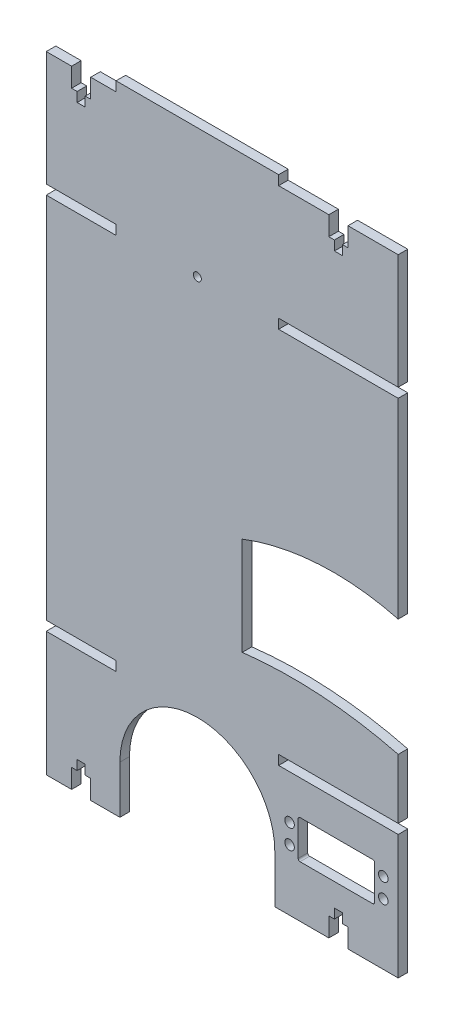
SolidWorks part; units mm, degrees
ref_plane "Front Plane" through (0, 0, 0) normal (0, 0, 1) x (1, 0, 0)
ref_plane "Top Plane" through (0, 0, 0) normal (0, 1, 0) x (1, 0, 0)
ref_plane "Right Plane" through (0, 0, 0) normal (1, 0, 0) x (0, 0, -1)
sketch "Sketch2" plane through (0, 0, 0) normal (0, 0, 1) x (1, 0, 0)
  line L1 (-92, 166.25) -> (92, 166.25)
  line L2 (-92, 166.25) -> (-92, -166.25)
  line L3 (-92, -166.25) -> (92, -166.25)
  line L4 (92, 166.25) -> (92, -166.25)
  line L5 (-92, 166.25) -> (92, -166.25) construction
  line L6 (-92, -166.25) -> (92, 166.25) construction
  point P0 (0, 0)
  dimension "D1" = 332.5
  dimension "D2" = 184
extrude "Boss-Extrude1" add sketch "Sketch2" along normal blind 5
sketch "Sketch3" plane through (0, 0, 5) normal (0, 0, 1) x (1, 0, 0)
  line L0 (-92, 166.25) -> (-92, -166.25) construction
  line L1 (-55.5, -101.25) -> (-92, -101.25)
  line L2 (-55.5, -101.25) -> (-55.5, -96.25)
  line L3 (-55.5, -96.25) -> (-92, -96.25)
  line L4 (-92, -101.25) -> (-92, -96.25)
  line L5 (-55.5, -101.25) -> (-92, -96.25) construction
  line L6 (-55.5, -96.25) -> (-92, -101.25) construction
  line L7 (-98, -96.25) -> (-55.5, -96.25) construction
  line L8 (92, -166.25) -> (92, 166.25) construction
  line L9 (29.5, -96.25) -> (92, -96.25)
  line L10 (29.5, -96.25) -> (29.5, -101.25)
  line L11 (29.5, -101.25) -> (92, -101.25)
  line L12 (92, -96.25) -> (92, -101.25)
  line L13 (29.5, -96.25) -> (92, -101.25) construction
  line L14 (29.5, -101.25) -> (92, -96.25) construction
  line L15 (29.5, -101.25) -> (92, -101.25) construction
  line L17 (29.5, 96.25) -> (92, 96.25) construction
  line L21 (-55.5, 161.25) -> (-92, 161.25)
  line L22 (-55.5, 161.25) -> (-55.5, 166.25)
  line L23 (-55.5, 166.25) -> (-92, 166.25)
  line L24 (-92, 161.25) -> (-92, 166.25)
  line L25 (-55.5, 161.25) -> (-92, 166.25) construction
  line L26 (-55.5, 166.25) -> (-92, 161.25) construction
  line L27 (29.5, 161.25) -> (92, 161.25)
  line L28 (29.5, 161.25) -> (29.5, 166.25)
  line L29 (29.5, 166.25) -> (92, 166.25)
  line L30 (92, 161.25) -> (92, 166.25)
  line L31 (29.5, 161.25) -> (92, 166.25) construction
  line L32 (29.5, 166.25) -> (92, 161.25) construction
  line L33 (29.5, 101.25) -> (92, 101.25)
  line L34 (27.5, -141.25) -> (27.5, -166.25)
  line L37 (-92, -166.25) -> (92, -166.25) construction
  line L38 (27.5, -166.25) -> (-53.5, -166.25)
  line L39 (-53.5, -166.25) -> (-53.5, -141.25)
  line L40 (29.5, 101.25) -> (29.5, 96.25)
  line L41 (29.5, 96.25) -> (92, 96.25)
  line L42 (92, 101.25) -> (92, 96.25)
  line L43 (29.5, 101.25) -> (92, 96.25) construction
  line L44 (29.5, 96.25) -> (92, 101.25) construction
  line L45 (-98, 101.25) -> (-55.5, 101.25) construction
  line L46 (-55.5, 96.25) -> (-92, 96.25)
  line L47 (-55.5, 96.25) -> (-55.5, 101.25)
  line L48 (-55.5, 101.25) -> (-92, 101.25)
  line L49 (-92, 96.25) -> (-92, 101.25)
  line L50 (-55.5, 96.25) -> (-92, 101.25) construction
  line L51 (-55.5, 101.25) -> (-92, 96.25) construction
  arc A2 (27.5, -141.25) -> (-53.5, -141.25) centre (-13, -141.25) ccw
  point P7 (-73.75, -98.75)
  point P17 (60.75, -98.75)
  point P32 (-73.75, 163.75)
  point P39 (60.75, 163.75)
  point P45 (60.75, 98.75)
  point P54 (-73.75, 98.75)
extrude "Cut-Extrude1" cut sketch "Sketch3" against normal blind 5
sketch "Sketch4" plane through (0, 0, 5) normal (0, 0, 1) x (1, 0, 0)
  line L0 (-73.75, 161.25) -> (-73.75, 123.1738) construction
  line L1 (-92, 161.25) -> (-55.5, 161.25) construction
  line L2 (69.7422, 161.25) -> (69.7422, -166.25) construction
  line L3 (-92, 0) -> (92, 0) construction
  line L5 (-13, 166.25) -> (-13, 111.1543) construction
  line L6 (29.5, 166.25) -> (-55.5, 166.25) construction
  line L7 (29.5, 161.25) -> (92, 161.25) construction
  line L8 (27.5, -166.25) -> (92, -166.25) construction
  line L9 (69.7422, -2.5) -> (44.3363, -2.5) construction
  line L10 (92, -96.25) -> (92, 96.25) construction
  line L11 (0, 0) -> (0, 111.1543) construction
  line L12 (0, 111.1543) -> (-13, 111.1543) construction
  line L13 (-6.5, 111.1543) -> (-6.5, 119.3244) construction
  line L14 (60.75, 161.25) -> (60.75, 140.689) construction
  line L15 (55.75, 161.25) -> (55.75, 151.25)
  line L16 (55.75, 151.25) -> (58.65, 151.25)
  line L17 (58.65, 151.25) -> (58.65, 146.25)
  line L18 (58.65, 146.25) -> (62.85, 146.25)
  line L19 (55.75, 161.25) -> (65.75, 161.25)
  line L20 (62.85, 151.25) -> (62.85, 146.25)
  line L21 (65.75, 151.25) -> (62.85, 151.25)
  line L22 (65.75, 161.25) -> (65.75, 151.25)
  line L23 (-78.75, 161.25) -> (-78.75, 151.25)
  line L24 (-78.75, 151.25) -> (-75.85, 151.25)
  line L25 (-75.85, 151.25) -> (-75.85, 146.25)
  line L26 (-68.75, 161.25) -> (-78.75, 161.25)
  line L27 (-71.65, 146.25) -> (-75.85, 146.25)
  line L28 (-71.65, 151.25) -> (-71.65, 146.25)
  line L29 (-68.75, 151.25) -> (-71.65, 151.25)
  line L30 (-68.75, 161.25) -> (-68.75, 151.25)
  line L31 (60.75, -166.25) -> (60.75, -145.689) construction
  line L32 (65.75, -166.25) -> (65.75, -156.25)
  line L33 (65.75, -156.25) -> (62.85, -156.25)
  line L34 (62.85, -156.25) -> (62.85, -151.25)
  line L35 (55.75, -166.25) -> (65.75, -166.25)
  line L36 (58.65, -151.25) -> (62.85, -151.25)
  line L37 (58.65, -156.25) -> (58.65, -151.25)
  line L38 (55.75, -156.25) -> (58.65, -156.25)
  line L39 (55.75, -166.25) -> (55.75, -156.25)
  line L40 (-68.75, -166.25) -> (-68.75, -156.25)
  line L41 (-68.75, -156.25) -> (-71.65, -156.25)
  line L42 (-71.65, -156.25) -> (-71.65, -151.25)
  line L43 (-71.65, -151.25) -> (-75.85, -151.25)
  line L44 (-68.75, -166.25) -> (-78.75, -166.25)
  line L45 (-75.85, -156.25) -> (-75.85, -151.25)
  line L46 (-78.75, -156.25) -> (-75.85, -156.25)
  line L47 (-78.75, -166.25) -> (-78.75, -156.25)
  point P36 (60.75, 146.25)
  point P46 (-73.75, 146.25)
  point P57 (60.75, -151.25)
  point P66 (-73.75, -151.25)
  dimension "D1" = 10
  dimension "D2" = 5
  dimension "D3" = 2.9
  dimension "D4" = 5
extrude "Cut-Extrude2" cut sketch "Sketch4" against normal blind 10
sketch "Sketch5" plane through (0, 0, 5) normal (0, 0, 1) x (1, 0, 0)
  line L0 (-55.5, 98.75) -> (29.5, 98.75) construction
  line L1 (-55.5, 96.25) -> (-55.5, 101.25) construction
  line L2 (29.5, 96.25) -> (29.5, 101.25) construction
  circle A0 centre (-13, 98.75) radius 2.1
  dimension "D1" = 4.2
extrude "Cut-Extrude3" cut sketch "Sketch5" against normal blind 10
sketch "Sketch6" plane through (0, 0, 0) normal (0, 0, -1) x (-1, 0, 0)
  line L0 (-78.2, -106.25) -> (-41.2, -106.25)
  line L1 (-41.2, -106.25) -> (-40.7, -106.25)
  line L2 (-39.7, -107.25) -> (-39.7, -125.25)
  line L3 (-40.7, -126.25) -> (-78.7, -126.25)
  line L4 (-79.7, -125.25) -> (-79.7, -107.25)
  line L5 (-78.7, -106.25) -> (-78.2, -106.25)
  circle A0 centre (-35.2, -111.17) radius 2.5
  circle A1 centre (-35.2, -121.33) radius 2.5
  circle A2 centre (-84.2, -111.17) radius 2.5
  circle A3 centre (-84.2, -121.33) radius 2.5
  arc A4 (-40.7, -106.25) -> (-39.7, -107.25) centre (-40.7, -107.25) cw
  arc A5 (-39.7, -125.25) -> (-40.7, -126.25) centre (-40.7, -125.25) cw
  arc A6 (-78.7, -126.25) -> (-79.7, -125.25) centre (-78.7, -125.25) cw
  arc A7 (-79.7, -107.25) -> (-78.7, -106.25) centre (-78.7, -107.25) cw
extrude "Cut-Extrude4" [suppressed] cut sketch "Sketch6" against normal blind 20
sketch "Sketch7" plane through (0, 0, 5) normal (0, 0, 1) x (1, 0, 0)
  line L4 (92.0183, -3.9595) -> (92, -22.8853)
  line L5 (92, -96.25) -> (92, 96.25) construction
  arc A4 (92.0183, -3.9595) -> (39.9761, 3.3554) centre (49.7, -116.25) ccw
  arc A5 (92, -22.8853) -> (36.0805, -14.6589) centre (49.7, -116.25) ccw
  arc A6 (39.9761, 3.3554) -> (36.0805, -14.6589) centre (102.0215, -19.4902) ccw
extrude "Cut-Extrude6" [suppressed] cut sketch "Sketch7" against normal through all
sketch "Esquisse1" plane through (0, 0, 0) normal (0, 0, -1) x (-1, 0, 0)
  line L0 (-84.2, -124.17) -> (-35.2, -124.17) construction
  line L1 (-84.2, -134.33) -> (-35.2, -134.33) construction
  line L2 (-29.5, -101.25) -> (-92, -101.25) construction
  line L4 (-40.7, -119.25) -> (-78.7, -119.25)
  line L5 (-39.7, -138.25) -> (-39.7, -120.25)
  line L6 (-78.7, -139.25) -> (-40.7, -139.25)
  line L7 (-79.7, -120.25) -> (-79.7, -138.25)
  circle A8 centre (-35.2, -134.33) radius 2.5
  circle A9 centre (-35.2, -124.17) radius 2.5
  circle A10 centre (-84.2, -134.33) radius 2.5
  circle A11 centre (-84.2, -124.17) radius 2.5
  arc A12 (-78.7, -119.25) -> (-79.7, -120.25) centre (-78.7, -120.25) ccw
  arc A13 (-39.7, -120.25) -> (-40.7, -119.25) centre (-40.7, -120.25) ccw
  arc A14 (-40.7, -139.25) -> (-39.7, -138.25) centre (-40.7, -138.25) ccw
  arc A15 (-79.7, -138.25) -> (-78.7, -139.25) centre (-78.7, -138.25) ccw
  dimension "D5" = 5
  dimension "D6" = 5
  dimension "D7" = 5
  dimension "D8" = 5
  dimension "D1" = 20
  dimension "D2" = 18
  dimension "D3" = 38
  dimension "D4" = 18
  dimension "D9" = 4.92
  dimension "D10" = 4.92
  dimension "D11" = 18
extrude "Enlèv. mat.-Extru.1" cut sketch "Esquisse1" against normal blind 10
sketch "Esquisse2" plane through (0, 0, 5) normal (0, 0, 1) x (1, 0, 0)
  line L0 (92, -59.5677) -> (10.4707, -59.5677) construction
  line L1 (10.4707, -8.2738) -> (10.4707, -59.5677)
  line L2 (92, -3.7504) -> (92, -64.9958)
  arc A0 (10.4707, -59.5677) -> (92, -64.9958) centre (36.6049, -282.026) cw
  arc A1 (10.4707, -8.2738) -> (92, -3.7504) centre (58.2719, -132.8388) cw
  point P3 (92, -57.1675)
  point P8 (92, -57.1675)
  point P9 (93.0204, -54.4045)
  point P10 (92, -3.7504)
  point P11 (92, -61.7724)
  point P12 (92, -64.9958)
extrude "Enlèv. mat.-Extru.2" cut sketch "Esquisse2" against normal blind 10
